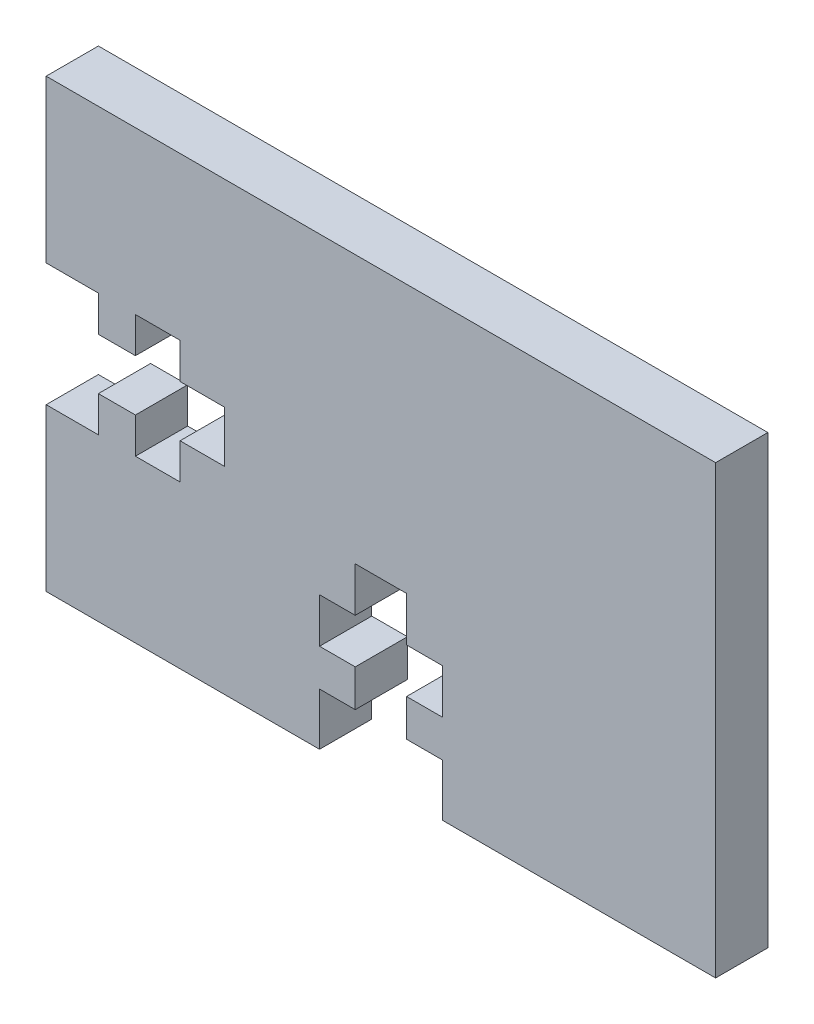
SolidWorks part; units mm, degrees
ref_plane "Front Plane" through (0, 0, 0) normal (0, 0, 1) x (1, 0, 0)
ref_plane "Top Plane" through (0, 0, 0) normal (0, 1, 0) x (1, 0, 0)
ref_plane "Right Plane" through (0, 0, 0) normal (1, 0, 0) x (0, 0, -1)
sketch "Sketch1" plane through (0, 0, 0) normal (0, 0, 1) x (1, 0, 0)
  line L0 (5.08, 14.1605) -> (2.9718, 14.1605)
  line L1 (0, 0) -> (38.1, 0)
  line L2 (0, 0) -> (0, 25.4)
  line L3 (0, 25.4) -> (38.1, 25.4)
  line L4 (38.1, 0) -> (38.1, 25.4)
  line L5 (5.08, 11.2395) -> (5.08, 9.2075)
  line L6 (5.08, 11.2395) -> (2.9718, 11.2395)
  line L7 (5.08, 14.1605) -> (5.08, 16.1925)
  line L8 (5.08, 16.1925) -> (7.62, 16.1925)
  line L9 (7.62, 16.1925) -> (7.62, 14.1605)
  line L10 (7.62, 14.1605) -> (10.16, 14.1605)
  line L11 (0, 12.7) -> (38.1, 12.7) construction
  line L12 (10.16, 14.1605) -> (10.16, 11.2395)
  line L13 (5.08, 9.2075) -> (7.62, 9.2075)
  line L14 (7.62, 9.2075) -> (7.62, 11.2395)
  line L15 (7.62, 11.2395) -> (10.16, 11.2395)
  line L16 (2.9718, 14.1605) -> (2.9718, 16.1925)
  line L17 (2.9718, 16.1925) -> (0, 16.1925)
  line L18 (2.9718, 11.2395) -> (2.9718, 9.2075)
  line L19 (2.9718, 9.2075) -> (0, 9.2075)
  line L20 (19.05, 25.4) -> (19.05, 0) construction
  line L21 (15.5575, 0) -> (15.5575, 2.9718)
  line L22 (15.5575, 2.9718) -> (17.5895, 2.9718)
  line L23 (17.5895, 2.9718) -> (17.5895, 5.08)
  line L24 (17.5895, 5.08) -> (15.5575, 5.08)
  line L25 (15.5575, 5.08) -> (15.5575, 7.62)
  line L26 (15.5575, 7.62) -> (17.5895, 7.62)
  line L27 (17.5895, 7.62) -> (17.5895, 10.16)
  line L28 (17.5895, 10.16) -> (20.5105, 10.16)
  line L29 (22.5425, 0) -> (22.5425, 2.9718)
  line L30 (22.5425, 2.9718) -> (20.5105, 2.9718)
  line L31 (20.5105, 2.9718) -> (20.5105, 5.08)
  line L32 (20.5105, 5.08) -> (22.5425, 5.08)
  line L33 (22.5425, 5.08) -> (22.5425, 7.62)
  line L34 (22.5425, 7.62) -> (20.5105, 7.62)
  line L35 (20.5105, 7.62) -> (20.5105, 10.16)
  point P20 (10.16, 12.7)
  point P43 (19.05, 10.16)
  dimension "D1" = 38.1
  dimension "D2" = 25.4
  dimension "D3" = 3.4925
  dimension "D4" = 10.16
  dimension "D5" = 1.4605
  dimension "D6" = 5.08
  dimension "D7" = 2.54
  dimension "D8" = 2.9718
  dimension "D9" = 1.4605
  dimension "D10" = 10.16
  dimension "D11" = 2.9718
  dimension "D12" = 3.4925
  dimension "D13" = 2.54
  dimension "D14" = 5.08
extrude "Boss-Extrude1" add sketch "Sketch1" along normal blind 2.9718 contours L35 L34 L33 L32 L31 L30 L29 L1 L4 L3 L2 L17 L16 L0 L7 L8 L9 L10 L12 L15 L14 L13 L5 L6 L18 L19 L21 L22 L23 L24 L25 L26 L27 L28
